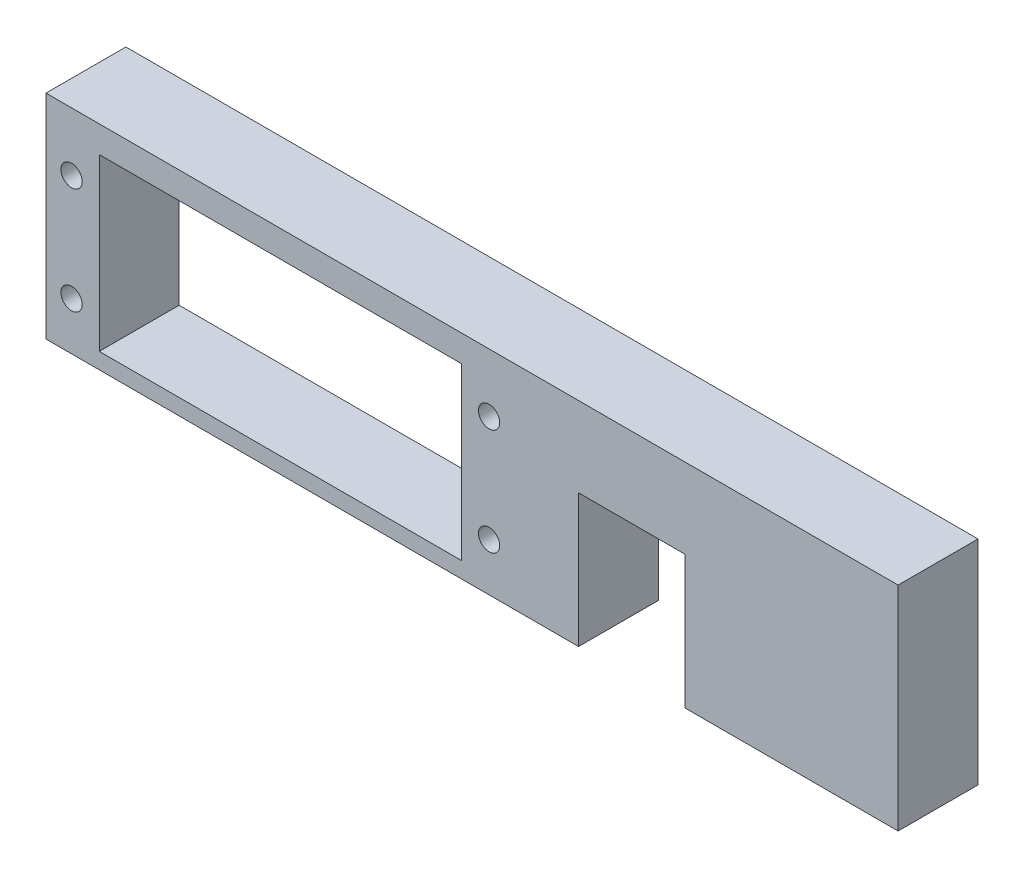
SolidWorks part; units mm, degrees
ref_plane "Front Plane" through (0, 0, 0) normal (0, 0, 1) x (1, 0, 0)
ref_plane "Top Plane" through (0, 0, 0) normal (0, 1, 0) x (1, 0, 0)
ref_plane "Right Plane" through (0, 0, 0) normal (1, 0, 0) x (0, 0, -1)
sketch "Sketch1" plane through (0, 0, 0) normal (0, 0, 1) x (1, 0, 0)
  line L0 (6.35, 12.065) -> (49.53, 12.065) construction
  line L1 (0, 0) -> (63.5, 0)
  line L2 (0, 0) -> (0, 25.4)
  line L3 (0, 25.4) -> (101.6, 25.4)
  line L4 (101.6, 0) -> (101.6, 25.4)
  line L5 (6.35, 22.225) -> (49.53, 22.225)
  line L6 (6.35, 22.225) -> (6.35, 1.905)
  line L7 (6.35, 1.905) -> (49.53, 1.905)
  line L8 (49.53, 22.225) -> (49.53, 1.905)
  line L9 (27.94, 22.225) -> (27.94, 1.905) construction
  line L10 (63.5, 0) -> (63.5, 15.875)
  line L11 (63.5, 15.875) -> (76.2, 15.875)
  line L12 (76.2, 15.875) -> (76.2, 0)
  line L13 (76.2, 0) -> (101.6, 0)
  circle A2 centre (3.048, 18.415) radius 1.27
  circle A3 centre (3.048, 5.715) radius 1.27
  circle A4 centre (52.832, 18.415) radius 1.27
  circle A5 centre (52.832, 5.715) radius 1.27
  dimension "D2" = 12.7
  dimension "D12" = 12.7
  dimension "D14" = 2.54
  dimension "D1" = 101.6
  dimension "D3" = 15.875
  dimension "D4" = 25.4
  dimension "D5" = 25.4
  dimension "D6" = 20.32
  dimension "D7" = 43.18
  dimension "D8" = 6.35
  dimension "D9" = 3.175
  dimension "D10" = 49.784
  dimension "D11" = 49.784
  dimension "D13" = 12.7
extrude "Boss-Extrude1" add sketch "Sketch1" along normal blind 9.525
sketch "Sketch2" plane through (0, 0, 0) normal (0, -1, 0) x (1, 0, 0)
  line L0 (101.6, 9.525) -> (101.6, 0) construction
  line L1 (0, 4.7625) -> (101.6, 4.7625) construction
  line L2 (0, 9.525) -> (0, 0) construction
  line L3 (0, 0) -> (63.5, 0) construction
  circle A0 centre (60.2488, 4.7625) radius 1.7272
  circle A1 centre (79.2988, 4.7625) radius 1.7272
  point P4 (101.6, 4.7625)
  dimension "D1" = 3.4544
  dimension "D2" = 19.05
  dimension "D3" = 22.3012
  dimension "D4" = 4.7625
extrude "Cut-Extrude1" cut sketch "Sketch2" against normal blind 12.7
